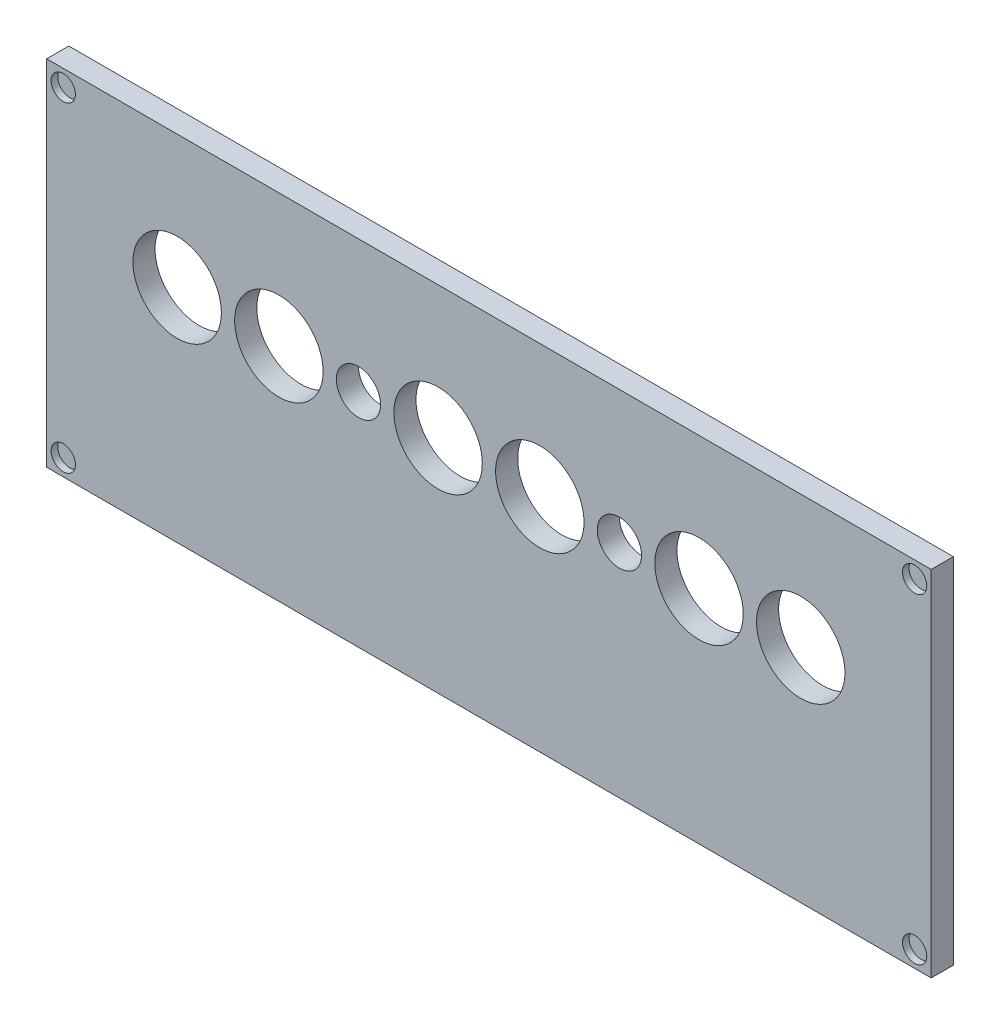
SolidWorks part; units mm, degrees
ref_plane "Alzado" through (0, 0, 0) normal (0, 0, 1) x (1, 0, 0)
ref_plane "Planta" through (0, 0, 0) normal (0, 1, 0) x (1, 0, 0)
ref_plane "Vista lateral" through (0, 0, 0) normal (1, 0, 0) x (0, 0, -1)
sketch "Croquis1" plane through (0, 0, 0) normal (0, 0, 1) x (1, 0, 0)
  line L1 (-100, -40) -> (100, -40)
  line L2 (-100, -40) -> (-100, 40)
  line L3 (-100, 40) -> (100, 40)
  line L4 (100, -40) -> (100, 40)
  line L5 (-100, -40) -> (100, 40) construction
  line L6 (-100, 40) -> (100, -40) construction
  point P0 (0, 0)
  dimension "D1" = 200
  dimension "D2" = 80
extrude "Saliente-Extruir1" add sketch "Croquis1" along normal blind 5
sketch "Croquis2" plane through (0, 0, 5) normal (0, 0, 1) x (1, 0, 0)
  line L0 (-100, 40) -> (-100, -40) construction
  line L1 (100, 40) -> (-100, 40) construction
  circle A0 centre (-96.25, 36.25) radius 2.75
  circle A1 centre (96.25, 36.25) radius 2.75
  circle A2 centre (96.25, -36.25) radius 2.75
  circle A3 centre (-96.25, -36.25) radius 2.75
  dimension "D1" = 5.5
  dimension "D2" = 3.75
  dimension "D3" = 3.75
  dimension "D4" = 2
  dimension "D5" = 2
extrude "Cortar-Extruir1" cut sketch "Croquis2" against normal blind 1.5 contours A0 | A3 | A2 | A1
sketch "Croquis4" plane through (0, 0, 5) normal (0, 0, 1) x (1, 0, 0)
  line L0 (-100, 0) -> (100, 0) construction
  line L1 (-100, 40) -> (-100, -40) construction
  line L2 (100, -40) -> (100, 40) construction
  line L3 (-100, 10) -> (100, 10) construction
  circle A0 centre (-70.5, 10) radius 10
  circle A1 centre (-47.5, 10) radius 10
  circle A2 centre (-29.5, 10) radius 5
  circle A3 centre (-11.5, 10) radius 10
  circle A4 centre (11.5, 10) radius 10
  circle A5 centre (29.5, 10) radius 5
  circle A6 centre (47.5, 10) radius 10
  circle A7 centre (70.5, 10) radius 10
  dimension "D2" = 20
  dimension "D3" = 20
  dimension "D4" = 10
  dimension "D5" = 20
  dimension "D6" = 20
  dimension "D7" = 10
  dimension "D8" = 20
  dimension "D9" = 20
  dimension "D1" = 10
  dimension "D10" = 29.5
  dimension "D11" = 23
  dimension "D12" = 18
  dimension "D13" = 18
  dimension "D14" = 23
  dimension "D15" = 18
  dimension "D16" = 18
  dimension "D17" = 23
extrude "Cortar-Extruir3" cut sketch "Croquis4" against normal blind 5
